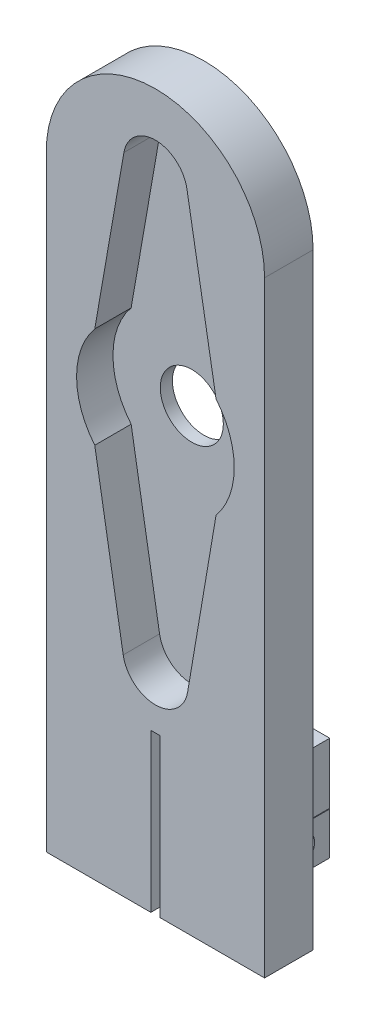
SolidWorks part; units mm, degrees
ref_plane "前基準面" through (0, 0, 0) normal (0, 0, 1) x (1, 0, 0)
ref_plane "上基準面" through (0, 0, 0) normal (0, 1, 0) x (1, 0, 0)
ref_plane "右基準面" through (0, 0, 0) normal (1, 0, 0) x (0, 0, -1)
sketch "草圖1" plane through (0, 0, 0) normal (0, 0, 1) x (1, 0, 0)
  line L0 (-9, 0) -> (-9, 50)
  line L1 (0, 45.5769) -> (0, 0) construction
  line L2 (-9, 0) -> (9, 0)
  line L3 (9, 0) -> (9, 50)
  arc A0 (-9, 50) -> (9, 50) centre (0, 50) cw
  dimension "D1" = 18
  dimension "D2" = 50
extrude "填料-伸長1" add sketch "草圖1" along normal blind 4 contours L3 A0 L0 L2
sketch "草圖2" plane through (0, 0, 4) normal (0, 0, 1) x (1, 0, 0)
  line L0 (-2.6, 53.1451) -> (-5, 39.3524)
  line L1 (2.6, 53.1451) -> (5, 39.3524)
  line L2 (-5, 31.0457) -> (-2.6563, 17.2433)
  line L3 (5, 31.0457) -> (2.6563, 17.2433)
  line L5 (0, 0) -> (0, 15) construction
  line L6 (0, 55.3318) -> (0, 46.5984) construction
  line L7 (0, 15.3887) -> (0, 39.6759) construction
  line L8 (-9, 0) -> (9, 0) construction
  arc A0 (-2.6563, 17.2433) -> (2.6563, 17.2433) centre (0, 17.6943) ccw
  arc A1 (2.6, 53.1451) -> (-2.6, 53.1451) centre (0, 52.6927) ccw
  arc A2 (5, 31.0457) -> (5, 39.3524) centre (0, 35.199) ccw
  arc A3 (-5, 39.3524) -> (-5, 31.0457) centre (0, 35.199) ccw
  dimension "D1" = 15
  dimension "D2" = 13
  dimension "D4" = 2.6
  dimension "D3" = 14
  dimension "D5" = 5
  dimension "D6" = 5
extrude "除料-伸長1" cut sketch "草圖2" against normal blind 3 contours L3 A0 L2 A3 L0 A1 L1 A2
sketch "草圖4" plane through (0, 0, 0) normal (0, 0, 1) x (1, 0, 0)
  line L0 (-9, 34.8563) -> (9, 34.8563) construction
  line L1 (-9, 0) -> (-9, 50) construction
  line L2 (9, 0) -> (9, 50) construction
  line L3 (0, 0) -> (0, 59) construction
  line L4 (0, 15.3887) -> (0, 39.6759) construction
  arc A0 (9, 50) -> (-9, 50) centre (0, 50) ccw construction
  circle A1 centre (0, 34.8563) radius 2.6
  dimension "D1" = 5.2
extrude "除料-伸長9" cut sketch "草圖4" against normal blind 2 and the other way blind 19
sketch "草圖5" plane through (0, 0, 0) normal (0, 0, 1) x (1, 0, 0)
  line L0 (0, 0) -> (0, 15) construction
  line L1 (-9, 0) -> (9, 0) construction
  line L11 (-0.375, 0) -> (0.375, 0)
  line L12 (-0.375, 0) -> (-0.375, 13)
  line L13 (-0.375, 13) -> (0.375, 13)
  line L14 (0.375, 0) -> (0.375, 13)
  arc A0 (-2.6563, 17.2433) -> (2.6563, 17.2433) centre (0, 17.6943) ccw construction
  point P12 (0, 7.9974)
  dimension "D1" = 0.75
  dimension "D2" = 13
extrude "除料-伸長11" cut sketch "草圖5" along normal through all contours L12 L13 L14 L11
sketch "草圖8" plane through (0, 0, 0) normal (0, 0, 1) x (1, 0, 0)
  line L0 (0.375, 0) -> (0.375, 13) construction
  line L1 (5.375, 10.8122) -> (0.375, 10.8122)
  line L2 (5.375, 10.8122) -> (5.375, 5.8122)
  line L3 (5.375, 5.8122) -> (0.375, 5.8122)
  line L4 (0.375, 10.8122) -> (0.375, 5.8122)
  dimension "D1" = 5
  dimension "D2" = 5
extrude "填料-伸長2" add sketch "草圖8" against normal blind 5
sketch "草圖9" plane through (0, 0, 0) normal (1, 0, 0) x (0, 0, -1)
  line L0 (0, 8.3122) -> (4.7595, 8.3122) construction
  line L1 (0, 5.8122) -> (0, 10.8122) construction
  line L2 (2.5, 5.8122) -> (2.5, 7.7398) construction
  line L3 (5, 5.8122) -> (0, 5.8122) construction
  circle A0 centre (2.3798, 8.3122) radius 1.25
  dimension "D1" = 2.5
extrude "除料-伸長12" cut sketch "草圖9" along normal blind 39
ref_plane "平面1" through (0.375, 0, 0) normal (1, 0, 0) x (0, 0, -1)
sketch "草圖11" plane through (0.375, 0, 0) normal (1, 0, 0) x (0, 0, -1)
  line L0 (0, 0) -> (0, 50) construction
  line L1 (0, 5.7622) -> (5, 5.7622)
  line L2 (0, 5.7622) -> (0, 2.2622)
  line L3 (0, 2.2622) -> (5, 2.2622)
  line L4 (5, 5.7622) -> (5, 2.2622)
  line L6 (2.5, 5.7622) -> (2.5, 2.2622) construction
  line L7 (5, 4.0122) -> (0, 4.0122) construction
  circle A0 centre (2.5, 4.0122) radius 1.25
  circle A2 centre (2.3798, 8.3122) radius 1.25 construction
  dimension "D1" = 2.5
  dimension "D3" = 1.8
  dimension "D2" = 5
  dimension "D4" = 3.5
extrude "填料-伸長4" add sketch "草圖11" along normal blind 5
